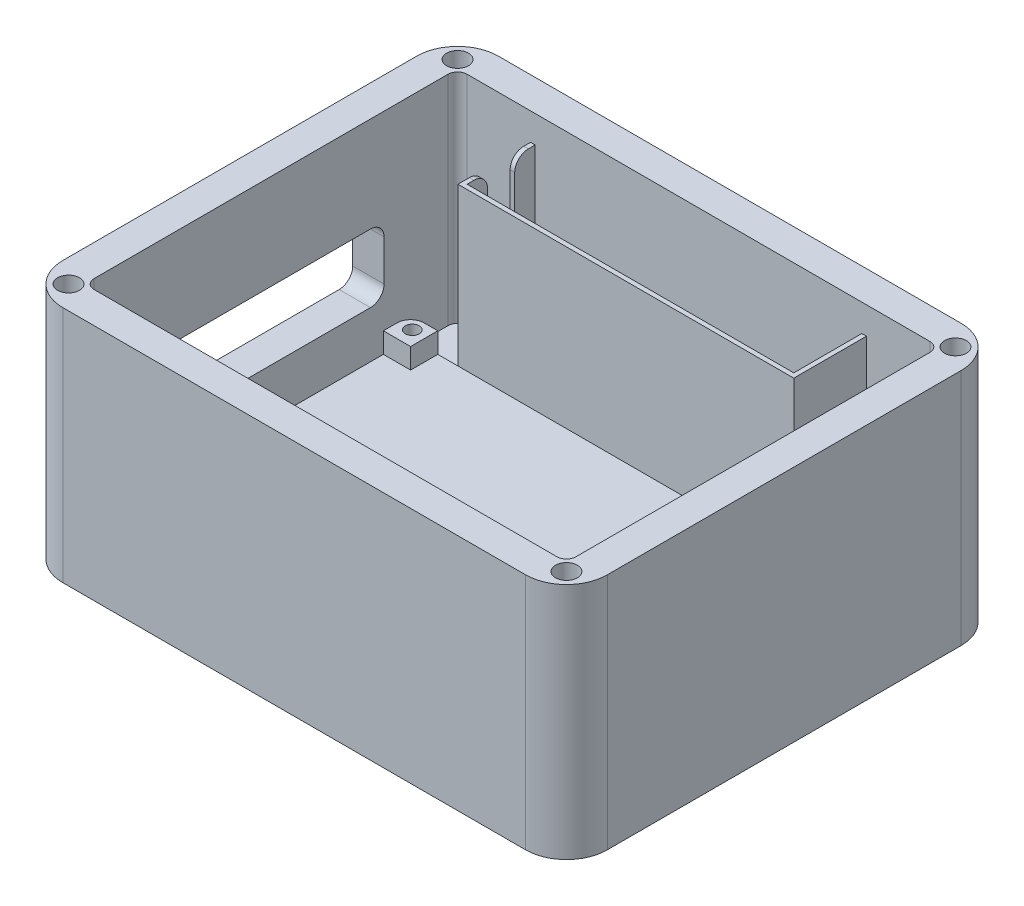
SolidWorks part; units mm, degrees
ref_plane "Front Plane" through (0, 0, 0) normal (0, 0, 1) x (1, 0, 0)
ref_plane "Top Plane" through (0, 0, 0) normal (0, 1, 0) x (1, 0, 0)
ref_plane "Right Plane" through (0, 0, 0) normal (1, 0, 0) x (0, 0, -1)
sketch "Sketch1" plane through (0, 0, 0) normal (0, 1, 0) x (1, 0, 0)
  line L1 (-53.975, 50.8) -> (53.975, 50.8)
  line L2 (-63.5, 41.275) -> (-63.5, -41.275)
  line L3 (-53.975, -50.8) -> (53.975, -50.8)
  line L4 (63.5, 41.275) -> (63.5, -41.275)
  line L5 (-63.5, 50.8) -> (63.5, -50.8) construction
  line L6 (-63.5, -50.8) -> (63.5, 50.8) construction
  arc A0 (-63.5, -41.275) -> (-53.975, -50.8) centre (-53.975, -41.275) ccw
  arc A1 (53.975, -50.8) -> (63.5, -41.275) centre (53.975, -41.275) ccw
  arc A2 (53.975, 50.8) -> (63.5, 41.275) centre (53.975, 41.275) cw
  arc A3 (-53.975, 50.8) -> (-63.5, 41.275) centre (-53.975, 41.275) ccw
  point P0 (0, 0)
  dimension "D3" = 9.525
  dimension "D1" = 127
  dimension "D2" = 101.6
extrude "Base_Plate" add sketch "Sketch1" along normal blind 4.7625
sketch "Sketch2" plane through (0, 4.7625, 0) normal (0, 1, 0) x (1, 0, 0)
  line L4 (-56.1975, 41.275) -> (-56.1975, -41.275)
  line L5 (-53.975, -43.4975) -> (53.975, -43.4975)
  line L6 (56.1975, -41.275) -> (56.1975, 41.275)
  line L7 (53.975, 43.4975) -> (-53.975, 43.4975)
  line L12 (-53.975, -50.8) -> (53.975, -50.8)
  line L13 (63.5, -41.275) -> (63.5, 41.275)
  line L14 (53.975, 50.8) -> (-53.975, 50.8)
  line L15 (-63.5, 41.275) -> (-63.5, -41.275)
  line L16 (-53.975, -50.8) -> (53.975, -50.8)
  line L17 (63.5, -41.275) -> (63.5, 41.275)
  line L18 (53.975, 50.8) -> (-53.975, 50.8)
  line L19 (-63.5, 41.275) -> (-63.5, -41.275)
  arc A0 (-56.1975, -41.275) -> (-53.975, -43.4975) centre (-53.975, -41.275) ccw
  arc A1 (53.975, -43.4975) -> (56.1975, -41.275) centre (53.975, -41.275) ccw
  arc A2 (56.1975, 41.275) -> (53.975, 43.4975) centre (53.975, 41.275) ccw
  arc A3 (-53.975, 43.4975) -> (-56.1975, 41.275) centre (-53.975, 41.275) ccw
  arc A4 (-63.5, -41.275) -> (-53.975, -50.8) centre (-53.975, -41.275) ccw
  arc A6 (53.975, -50.8) -> (63.5, -41.275) centre (53.975, -41.275) ccw
  arc A8 (63.5, 41.275) -> (53.975, 50.8) centre (53.975, 41.275) ccw
  arc A10 (-53.975, 50.8) -> (-63.5, 41.275) centre (-53.975, 41.275) ccw
  arc A12 (-63.5, -41.275) -> (-53.975, -50.8) centre (-53.975, -41.275) ccw
  arc A13 (53.975, -50.8) -> (63.5, -41.275) centre (53.975, -41.275) ccw
  arc A14 (63.5, 41.275) -> (53.975, 50.8) centre (53.975, 41.275) ccw
  arc A15 (-53.975, 50.8) -> (-63.5, 41.275) centre (-53.975, 41.275) ccw
  dimension "D1" = 0
  dimension "D2" = 7.3025
extrude "OutsideBoss" add sketch "Sketch2" along normal blind 50.8
hole_wizard "TopPlate_MountingHole_#8 (0.199) Diameter Hole1" positions "Sketch4" profile "Sketch7" hole size "#10" standard "ANSI Inch" end condition through all
sketch "Sketch4" plane through (0, 0, 0) normal (0, -1, 0) x (-1, 0, 0)
  line L0 (-63.5, -41.275) -> (-63.5, 41.275) construction
  line L1 (-53.975, 50.8) -> (53.975, 50.8) construction
  line L2 (53.975, -50.8) -> (-53.975, -50.8) construction
  line L3 (63.5, 41.275) -> (63.5, -41.275) construction
  line L4 (58.0707, 45.3708) -> (-58.0708, 45.3708) construction
  line L5 (-58.0708, 45.3708) -> (-58.0707, -45.3707) construction
  line L6 (-58.0707, -45.3707) -> (58.0707, -45.3707) construction
  line L7 (58.0707, -45.3707) -> (58.0707, 45.3708) construction
  point P2 (-58.0708, 45.3708)
  point P4 (58.0707, -45.3707)
  point P15 (-58.0707, -45.3707)
  point P17 (58.0707, 45.3708)
  dimension "D1" = 5.4292
  dimension "D2" = 5.4292
  dimension "D3" = 5.4292
  dimension "D4" = 5.4292
sketch "Sketch7" plane through (58.0708, 0, -45.3708) normal (1, 0, 0) x (0, 0, -1)
  line L0 (0, 0) -> (0, 55.5625)
  line L1 (0, 55.5625) -> (2.5527, 55.5625)
  line L2 (2.5527, 55.5625) -> (2.5527, 0)
  line L5 (2.5527, 0) -> (0, 0)
  line L11 (0, -6.35) -> (0, 107.95) construction
  dimension "Thru Hole Dia." = 5.1054
  dimension "Thru Hole Depth" = 55.5625
sketch "Sketch8" plane through (0, 4.7625, 0) normal (0, 1, 0) x (1, 0, 0)
  line L0 (-56.1975, 41.275) -> (-56.1975, -41.275) construction
  line L1 (46.8312, -37.1475) -> (-46.8312, -37.1475)
  line L2 (50.0063, -33.9725) -> (50.0063, 23.1775)
  line L3 (46.8312, 26.3525) -> (-46.8312, 26.3525)
  line L4 (-50.0063, -33.9725) -> (-50.0062, 23.1775)
  line L5 (50.0063, -37.1475) -> (-50.0062, 26.3525) construction
  line L6 (50.0063, 26.3525) -> (-50.0063, -37.1475) construction
  line L7 (-53.975, -43.4975) -> (53.975, -43.4975) construction
  arc A0 (46.8312, -37.1475) -> (50.0063, -33.9725) centre (46.8313, -33.9725) ccw
  arc A1 (50.0063, 23.1775) -> (46.8312, 26.3525) centre (46.8313, 23.1775) ccw
  arc A2 (-46.8312, 26.3525) -> (-50.0062, 23.1775) centre (-46.8312, 23.1775) ccw
  arc A3 (-50.0063, -33.9725) -> (-46.8312, -37.1475) centre (-46.8313, -33.9725) ccw
  dimension "D5" = 3.175
  dimension "D1" = 100.0125
  dimension "D2" = 63.5
  dimension "D3" = 6.1912
  dimension "D4" = 6.35
extrude "PCB_Plate" add sketch "Sketch8" along normal blind 12.7
hole_wizard "#4 Clearance Hole1" positions "Sketch9" profile "Sketch10" hole size "#4" standard "ANSI Inch"
sketch "Sketch9" plane through (0, 17.4625, 0) normal (0, 1, 0) x (1, 0, 0)
  line L0 (0, -5.3975) -> (46.8312, -5.3975) construction
  line L1 (46.8312, -5.3975) -> (46.8312, 23.5744) construction
  line L3 (0, -5.3975) -> (0, 26.3525) construction
  line L4 (46.8312, 26.3525) -> (-46.8312, 26.3525) construction
  line L6 (0, -5.3975) -> (0, -37.1475) construction
  line L7 (-46.8312, -37.1475) -> (46.8312, -37.1475) construction
  line L9 (46.8312, -5.3975) -> (46.8313, -34.3694) construction
  line L11 (0, -5.3975) -> (-46.8312, -5.3975) construction
  line L12 (-46.8312, -5.3975) -> (-46.8313, 23.5744) construction
  line L14 (-46.8312, -5.3975) -> (-46.8312, -34.3694) construction
  point P0 (-46.8313, 23.5744)
  point P2 (46.8312, 23.5744)
  point P4 (-46.8312, -34.3694)
  point P6 (46.8313, -34.3694)
  dimension "D1" = 93.6625
  dimension "D2" = 57.9437
sketch "Sketch10" plane through (-46.8313, 17.4625, -23.5744) normal (1, 0, 0) x (0, 0, 1)
  line L0 (0, 0) -> (0, 16.9826)
  line L1 (0, 16.9826) -> (1.6319, 16.002)
  line L2 (1.6319, 16.002) -> (1.6319, 0)
  line L5 (1.6319, 0) -> (0, 0)
  line L10 (0, 16.9826) -> (-1.632, 16.002) construction
  line L11 (0, -6.35) -> (0, 107.95) construction
  dimension "Hole Dia." = 3.2639
  dimension "Hole Depth" = 16.002
  dimension "Drill Angle" = 118
sketch "Sketch11" plane through (0, 17.4625, 0) normal (0, 1, 0) x (1, 0, 0)
  line L0 (46.8312, 26.3525) -> (-46.8312, 26.3525) construction
  line L1 (-43.6562, 42.5728) -> (43.6562, 42.5728)
  line L2 (-43.6562, 42.5728) -> (-43.6562, -42.5728)
  line L3 (-43.6562, -42.5728) -> (43.6562, -42.5728)
  line L4 (43.6562, 42.5728) -> (43.6562, -42.5728)
  line L5 (-43.6562, 42.5728) -> (43.6562, -42.5728) construction
  line L6 (-43.6562, -42.5728) -> (43.6562, 42.5728) construction
  line L7 (-52.7272, 20.0025) -> (52.7272, 20.0025)
  line L8 (-52.7272, 20.0025) -> (-52.7272, -30.7975)
  line L9 (-52.7272, -30.7975) -> (52.7272, -30.7975)
  line L10 (52.7272, 20.0025) -> (52.7272, -30.7975)
  line L11 (-52.7272, 20.0025) -> (52.7272, -30.7975) construction
  line L12 (-52.7272, -30.7975) -> (52.7272, 20.0025) construction
  line L13 (-46.8312, -37.1475) -> (46.8312, -37.1475) construction
  line L14 (-50.0062, 23.1775) -> (-50.0062, -33.9725) construction
  point P0 (0, 0)
  point P6 (0, -5.3975)
  line M9 (-50.0062, 23.1775) -> (-50.0063, -33.9725)
  line M10 (-46.8312, -37.1475) -> (46.8312, -37.1475)
  line M11 (50.0063, -33.9725) -> (50.0063, 23.1775)
  line M12 (46.8312, 26.3525) -> (-46.8312, 26.3525)
  dimension "D1" = 6.35
  dimension "D2" = 6.35
  dimension "D3" = 6.35
extrude "Cut-Extrude2" cut sketch "Sketch11" against normal blind 4.7625 contours L2 L9 L4 L7 | L4 L9 L7 M11 | L2 L7 L4 M12 | L9 L2 L4 M10 | L9 L2 L7 M9
sketch "Sketch12" plane through (0, 4.7625, 0) normal (0, 1, 0) x (1, 0, 0)
  line L0 (0, 43.4975) -> (0, 27.6225) construction
  line L1 (53.975, 43.4975) -> (-53.975, 43.4975) construction
  line L2 (-39.1668, 26.5557) -> (-39.1668, 44.5643)
  line L3 (-38.1, 27.6225) -> (38.1, 27.6225)
  line L4 (-38.1, 27.6225) -> (-38.1, 43.4975)
  line L5 (-38.1, 43.4975) -> (38.1, 43.4975)
  line L6 (38.1, 27.6225) -> (38.1, 43.4975)
  line L7 (-38.1, 27.6225) -> (38.1, 43.4975) construction
  line L8 (-38.1, 43.4975) -> (38.1, 27.6225) construction
  line L9 (-39.1668, 44.5643) -> (39.1668, 44.5643)
  line L10 (39.1668, 26.5557) -> (39.1668, 44.5643)
  line L11 (-39.1668, 26.5557) -> (39.1668, 26.5557)
  point P5 (0, 35.56)
  dimension "D1" = 15.875
  dimension "D2" = 76.2
  dimension "D3" = 1.0668
extrude "BatteryHolder" add sketch "Sketch12" along normal offset from surface (44.45 mm away) 6.35 up to face at (58.0708, 55.5625, -47.9235)
sketch "Sketch13" plane through (-38.1, 0, 0) normal (1, 0, 0) x (0, 0, -1)
  line L0 (43.4975, 49.2125) -> (27.6225, 49.2125) construction
  line L1 (38.735, 74.6125) -> (32.385, 74.6125)
  line L2 (38.735, 74.6125) -> (38.735, 23.8125)
  line L3 (38.735, 23.8125) -> (32.385, 23.8125)
  line L4 (32.385, 74.6125) -> (32.385, 23.8125)
  line L5 (38.735, 74.6125) -> (32.385, 23.8125) construction
  line L6 (38.735, 23.8125) -> (32.385, 74.6125) construction
  circle A0 centre (35.56, 23.8125) radius 3.175
  point P0 (35.56, 49.2125)
  line M5 (43.4975, 49.2125) -> (27.6225, 49.2125)
  dimension "D1" = 6.35
  dimension "D2" = 25.4
extrude "BatteryLeadFeader" cut sketch "Sketch13" against normal up to next contours A0 L2 L4 M5 | L3 A0 | L3 A0
fillet "BatteryLeadFillets" radius 3.175 2 edges at (-38.6334, 49.2125, -38.735) (-38.6334, 49.2125, -32.385)
sketch "Sketch14" plane through (-63.5, 0, 0) normal (-1, 0, 0) x (0, 0, 1)
  line L0 (-26.3525, 17.4625) -> (-20.0025, 17.4625) construction
  line L1 (30.7975, 17.4625) -> (37.1475, 17.4625) construction
  line L2 (-26.3525, 17.4625) -> (-20.0025, 17.4625) construction
  line L3 (30.7975, 17.4625) -> (37.1475, 17.4625) construction
  line L4 (30.7975, 17.4625) -> (-20.0025, 17.4625) construction
  line L5 (-26.3525, 20.6375) -> (-26.3525, 30.1625)
  line L6 (-23.1775, 33.3375) -> (33.9725, 33.3375)
  line L7 (37.1475, 30.1625) -> (37.1475, 20.6375)
  line L8 (33.9725, 17.4625) -> (-23.1775, 17.4625)
  arc A0 (-26.3525, 20.6375) -> (-23.1775, 17.4625) centre (-23.1775, 20.6375) ccw
  arc A1 (33.9725, 17.4625) -> (37.1475, 20.6375) centre (33.9725, 20.6375) ccw
  arc A2 (37.1475, 30.1625) -> (33.9725, 33.3375) centre (33.9725, 30.1625) ccw
  arc A3 (-23.1775, 33.3375) -> (-26.3525, 30.1625) centre (-23.1775, 30.1625) ccw
  point P16 (-26.3525, 33.3375)
  dimension "D2" = 3.175
  dimension "D1" = 15.875
extrude "Cut-Extrude3" cut sketch "Sketch14" against normal up to next
